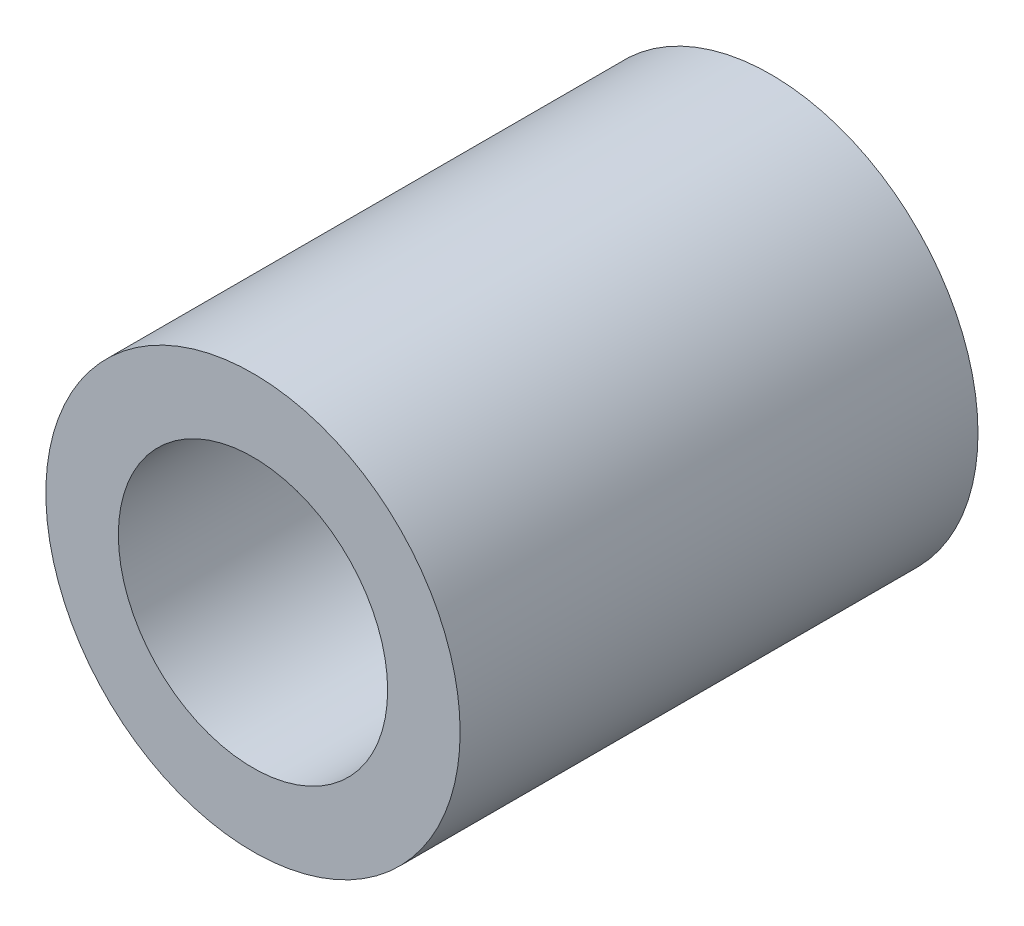
SolidWorks part; units mm, degrees
ref_plane "Front Plane" through (0, 0, 0) normal (0, 0, 1) x (1, 0, 0)
ref_plane "Top Plane" through (0, 0, 0) normal (0, 1, 0) x (1, 0, 0)
ref_plane "Right Plane" through (0, 0, 0) normal (1, 0, 0) x (0, 0, -1)
sketch "Sketch1" plane through (0, 0, 0) normal (0, 0, 1) x (1, 0, 0)
  circle A0 centre (0, 0) radius 2
  dimension "D1" = 4
extrude "Boss-Extrude1" add sketch "Sketch1" against normal blind 5
sketch "Sketch2" plane through (0, 0, 0) normal (0, 0, 1) x (1, 0, 0)
  circle A0 centre (0, 0) radius 1.3
  dimension "D1" = 2.6
extrude "Cut-Extrude1" cut sketch "Sketch2" against normal through all
